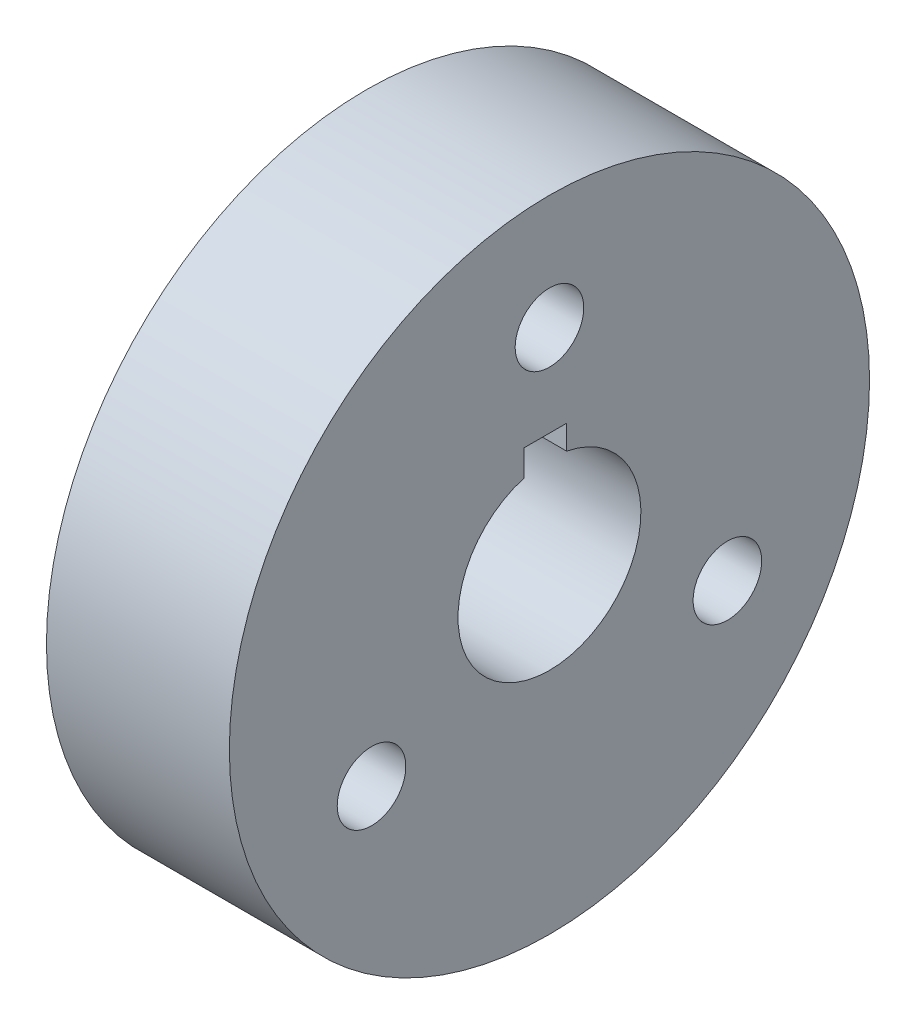
SolidWorks part; units mm, degrees
ref_plane "Front Plane" through (0, 0, 0) normal (0, 0, 1) x (1, 0, 0)
ref_plane "Top Plane" through (0, 0, 0) normal (0, 1, 0) x (1, 0, 0)
ref_plane "Right Plane" through (0, 0, 0) normal (1, 0, 0) x (0, 0, -1)
sketch "Sketch1" plane through (0, 0, 0) normal (0, 0, 1) x (1, 0, 0)
  line L0 (-22.5233, 13.4225) -> (-22.5233, -16.5775)
  line L1 (-22.5233, -16.5775) -> (37.4767, -16.5775)
  line L2 (37.4767, -16.5775) -> (37.4767, 53.4225)
  line L3 (37.4767, 53.4225) -> (-2.5233, 53.4225)
  line L4 (-2.5233, 53.4225) -> (-2.5233, 43.4225)
  line L5 (-2.5233, 43.4225) -> (17.4767, 43.4225)
  line L6 (17.4767, 43.4225) -> (17.4767, 13.4225)
  line L7 (17.4767, 13.4225) -> (-22.5233, 13.4225)
  dimension "D1" = 20
  dimension "D2" = 40
  dimension "D3" = 60
  dimension "D4" = 30
  dimension "D5" = 70
  dimension "D6" = 60
revolve "Revolve1" add sketch "Sketch1" angle 360 about L1
sketch "Sketch2" plane through (-22.5233, 0, 0) normal (-1, 0, 0) x (0, 0, 1)
  line L0 (-3.7632, 3.0652) -> (-3.7632, 8.3544)
  line L1 (-3.7632, 8.3544) -> (5.5756, 8.3544)
  line L2 (5.5756, 8.3544) -> (5.5756, 2.6296)
  circle A2 centre (0, -16.5775) radius 20
  arc A3 (-3.7632, 3.0652) -> (5.5756, 2.6296) centre (0, -16.5775) ccw
  point P2 (-3.7632, 3.0652)
  dimension "D1" = 10
extrude "Cut-Extrude1" cut sketch "Sketch2" against normal through all
sketch "Sketch3" plane through (17.4767, 0, 0) normal (-1, 0, 0) x (0, 0, 1)
  line L0 (5.5756, 8.3544) -> (-3.7632, 8.3544) construction
  circle A0 centre (0, 28.3544) radius 7.5
  dimension "D1" = 15
  dimension "D2" = 20
extrude "Cut-Extrude2" cut sketch "Sketch3" against normal through all
pattern_circular "CirPattern1" count 3 over 360 about axis through (0, -16.5775, 0) along (1, 0, 0) of "Cut-Extrude2"
